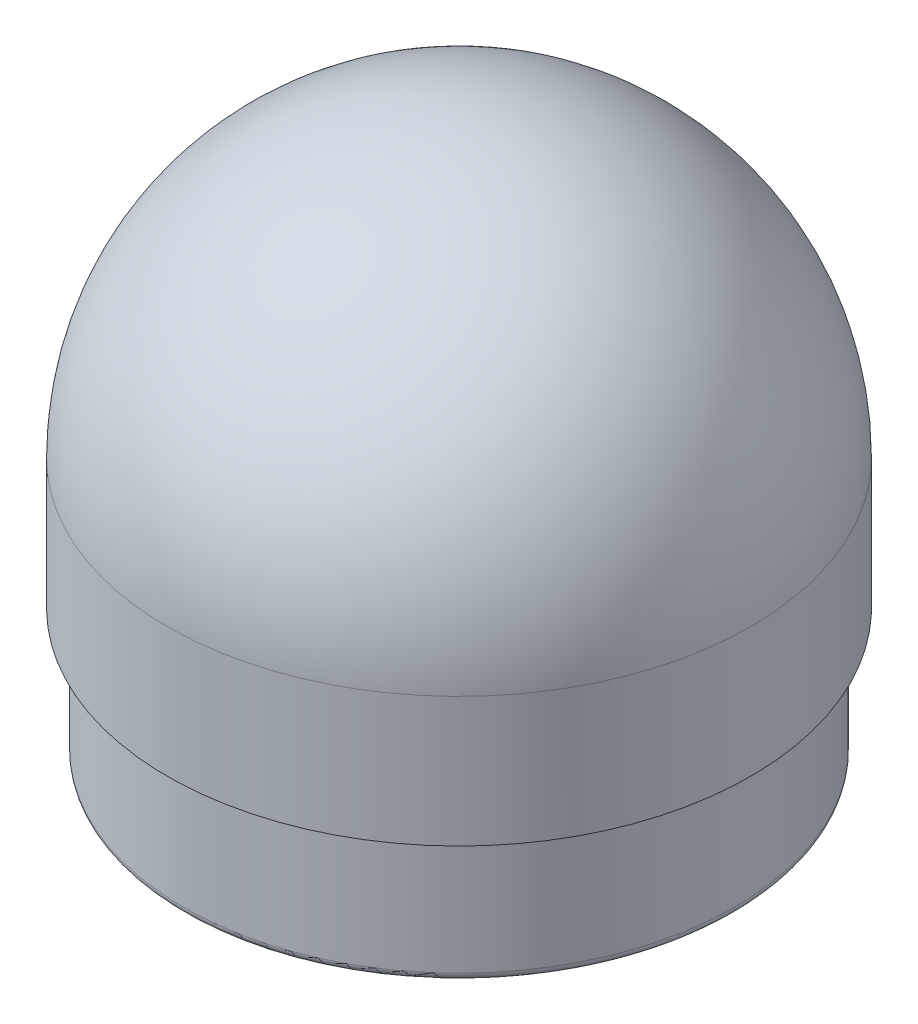
SolidWorks part; units mm, degrees
ref_plane "Front Plane" through (0, 0, 0) normal (0, 0, 1) x (1, 0, 0)
ref_plane "Top Plane" through (0, 0, 0) normal (0, 1, 0) x (1, 0, 0)
ref_plane "Right Plane" through (0, 0, 0) normal (1, 0, 0) x (0, 0, -1)
sketch "Sketch2" plane through (0, 0, 0) normal (0, 0, 1) x (1, 0, 0)
  line L0 (47.625, 0) -> (52.3875, 0)
  line L1 (53.975, 1.5875) -> (53.975, 25.4)
  line L2 (53.975, 25.4) -> (57.15, 25.4)
  line L3 (57.15, 25.4) -> (57.15, 50.8)
  line L5 (47.625, 50.8) -> (47.625, 0)
  line L6 (0, 98.425) -> (0, 107.95)
  arc A0 (52.3875, 0) -> (53.975, 1.5875) centre (52.3875, 1.5875) ccw
  arc A1 (47.625, 50.8) -> (0, 98.425) centre (0, 50.8) ccw
  arc A2 (57.15, 50.8) -> (0, 107.95) centre (0, 50.8) ccw
  dimension "D3" = 1.5875
  dimension "D1" = 57.15
  dimension "D2" = 47.625
  dimension "D4" = 25.4
  dimension "D5" = 50.8
  dimension "D6" = 6.35
  dimension "D7" = 23.8125
revolve "Revolve1" add sketch "Sketch2" angle 360 about L6
